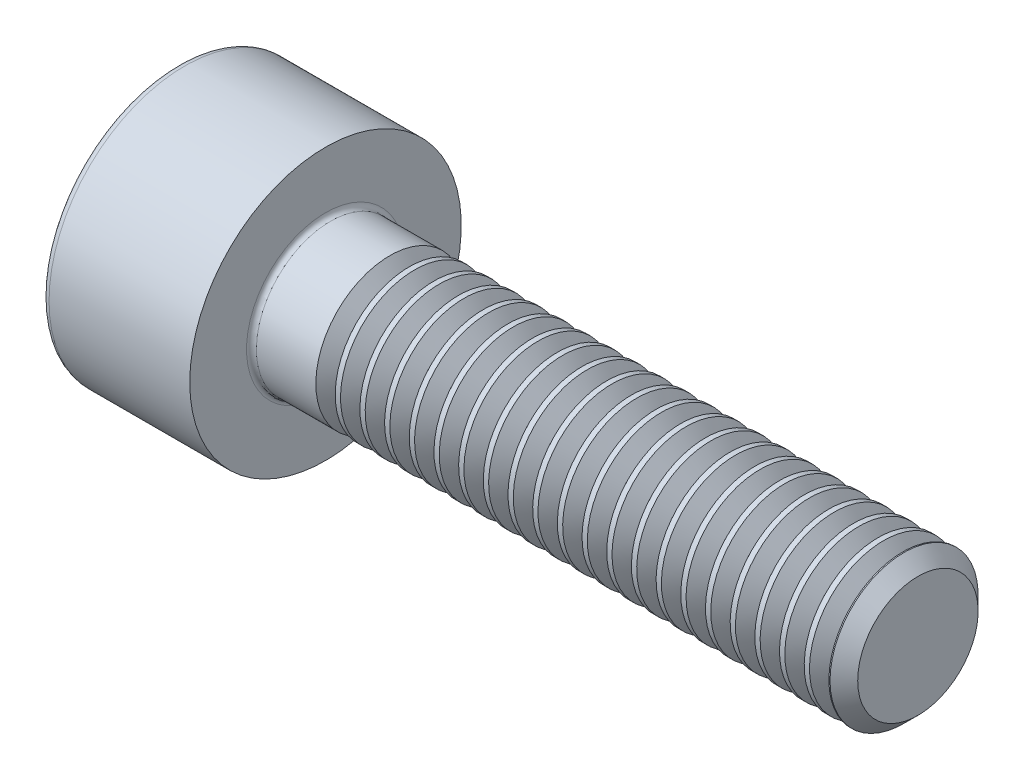
SolidWorks part; units mm, degrees
revolve "Base-Revolve" add sketch "BodySke"
sketch "BodySke" plane through (0, 0, 0) normal (0, 0, 1) x (1, 0, 0)
  line L0 (0, 0) -> (0, 2.75)
  line L1 (0, 2.75) -> (3, 2.75)
  line L2 (3, 2.75) -> (3, 1.5)
  line L3 (3, 1.5) -> (14.7195, 1.5)
  line L4 (15, 1.2195) -> (15, 0)
  line L5 (15, 0) -> (0, 0)
  line L6 (-31.75, 0) -> (127, 0) construction
  line L8 (15, 1.2195) -> (14.7195, 1.5)
  line L10 (15, -1.2195) -> (14.7195, -1.5) construction
  line L11 (3.5, 9.525) -> (3.5, 3.175) construction
  line L12 (3, 9.525) -> (3, 3.175) construction
  line L13 (-45, 9.525) -> (-45, 3.175) construction
  dimension "Head_ht" = 3
  dimension "Length" = 12
  dimension "Body_ch_ang" = 45
  dimension "Diameter" = 3
  dimension "Minor_dia" = 2.439
  dimension "Advance" = 0.5
  dimension "Thread_nom" = 12
  dimension "Thread_length" = 60
  dimension "Head_dia" = 5.5
cosmetic thread "ThreadCosmetic" [suppressed]
fillet "Fillet1" radius 0.1 1 edges at (3, 0, 1.5)
fillet "Fillet2" radius 0.15 1 edges at (0, 0, 2.75)
ref_plane "Plane1" through (0, 0, 0) normal (0, 0, 1) x (1, 0, 0)
ref_plane "Plane2" through (0, 0, 0) normal (0, 1, 0) x (1, 0, 0)
ref_plane "Plane3" through (0, 0, 0) normal (1, 0, 0) x (0, 0, -1)
sketch "Sketch2" plane through (0, 0, 0) normal (0, 0, 1) x (1, 0, 0)
  line L0 (0, 1.28) -> (1.3, 1.28)
  line L1 (1.3, 1.28) -> (2.039, 0)
  line L2 (-31.75, 0) -> (127, 0) construction
  line L3 (2.039, 0) -> (0, 0)
  line L4 (0, 0) -> (0, 1.28)
  line L6 (0, 0) -> (47.625, 0) construction
  dimension "D1" = 1.28
  dimension "D2" = 60
  dimension "Depth" = 1.3
revolve "Hex-PreBroach" cut sketch "Sketch2" angle 360 about L6
sketch "Sketch3" plane through (0, 0, 0) normal (-1, 0, 0) x (0, 0.5, 0.866)
  line L0 (0.739, 1.28) -> (-0.739, 1.28)
  line L1 (-0.739, 1.28) -> (-1.478, 0)
  line L2 (0.739, 1.28) -> (1.478, 0)
  line L3 (0.739, -1.28) -> (1.478, 0)
  line L4 (0.739, -1.28) -> (-0.739, -1.28)
  line L5 (-0.739, -1.28) -> (-1.478, 0)
  dimension "D1" = 1.28
  dimension "D2" = 1.28
  dimension "Hex_size" = 2.56
extrude "Hex" cut sketch "Sketch3" against normal blind 1.3
sketch "ThdSchSke" plane through (0, 0, 0) normal (0, 0, 1) x (1, 0, 0)
  line L0 (4.5, -1.2195) -> (4.3036, -1.5)
  line L1 (4.5, -1.2195) -> (4.6964, -1.5)
  line L2 (4.6964, -1.5) -> (4.6964, -1.875)
  line L3 (-3.175, 0) -> (5.1513, 0) construction
  line L4 (0, 2.6) -> (0, -2.6) construction
  line L5 (4.6964, -1.875) -> (4.3036, -1.875)
  line L6 (4.3036, -1.875) -> (4.3036, -1.5)
  dimension "Thread_minor" = 2.439
  dimension "Diameter" = 3
  dimension "Start" = 4.5
revolve "ThreadSchematic" cut sketch "ThdSchSke" angle 360 about L3
pattern_linear "ThdSchPat" count 21 spacing 0.5 along (1, 0, 0) of "ThreadSchematic"
equation "\"D2@Sketch3\" = \"Hex_size@Sketch3\" / 2"
equation "\"D1@Sketch3\" = \"Hex_size@Sketch3\" / 2"
equation "\"D1@Sketch2\" = \"Hex_size@Sketch3\" / 2"
equation "\"Thread_minor@ThreadCosmetic\"  =  \"Minor_dia@BodySke\""
equation "\"Depth@Sketch2\" =  \"Key_eng@Hex\""
equation "\"Thread_length@ThreadCosmetic\" = ((sgn( (\"Length@BodySke\" - \"Advance@BodySke\" * 3.0) - \"Thread_nom@BodySke\" )-1)*( (\"Length@BodySke\" - \"Advance@BodySke\" * 3.0) - \"Thread_nom@BodySke\" ))/-2+ \"Thread_nom@BodySke\""
equation "\"Thread_minor@ThdSchSke\" = \"Minor_dia@BodySke\""
equation "\"Diameter@ThdSchSke\" = \"Diameter@BodySke\""
equation "\"Overcut@ThdSchSke\" = \"Diameter@BodySke\" * 1.25"
equation "\"Start@ThdSchSke\" = \"Head_ht@BodySke\" + \"Length@BodySke\" - \"Thread_length@ThreadCosmetic\"  '---Non-countersunk---"
equation "\"Num_threads@ThdSchPat\" = int( \"Thread_length@ThreadCosmetic\" / \"Advance@BodySke\" + 0.999 )  + 1"
equation "\"Advance@ThdSchPat\" = \"Thread_length@ThreadCosmetic\" /  (\"Num_threads@ThdSchPat\" - 1) 'relax it"
equation "\"Num_threads@ThdSchPat\" = \"Num_threads@ThdSchPat\" - sgn( \"Num_threads@ThdSchPat\" - 1) '---chamfered tips only---"
